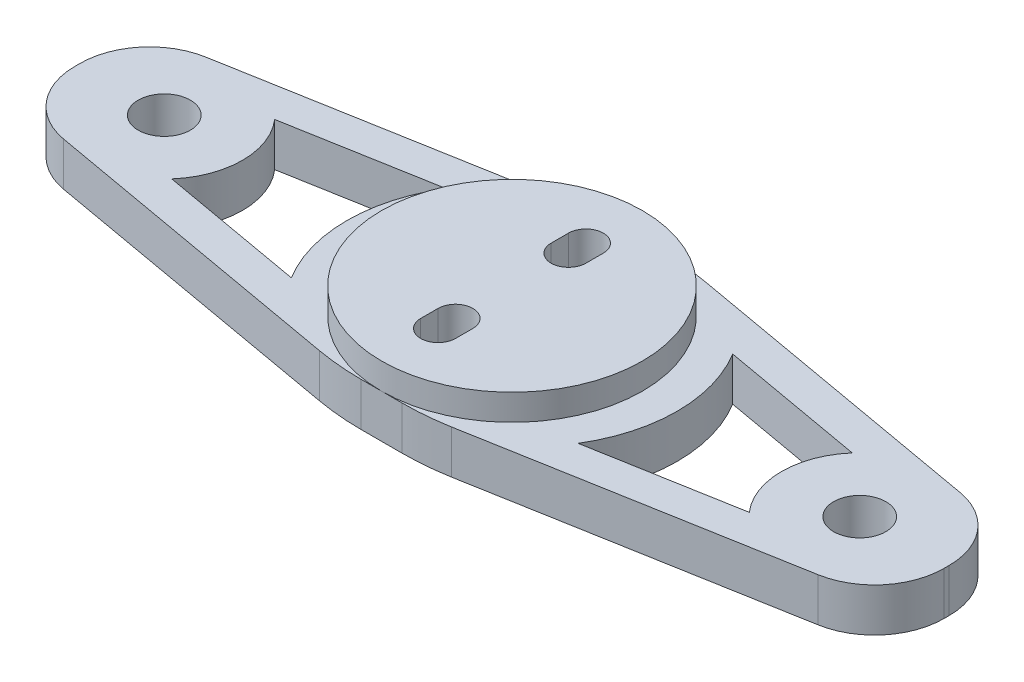
SolidWorks part; units mm, degrees
ref_plane "Front Plane" through (0, 0, 0) normal (0, 0, 1) x (1, 0, 0)
ref_plane "Top Plane" through (0, 0, 0) normal (0, 1, 0) x (1, 0, 0)
ref_plane "Right Plane" through (0, 0, 0) normal (1, 0, 0) x (0, 0, -1)
sketch "Sketch1" plane through (0, 0, 0) normal (0, 1, 0) x (1, 0, 0)
  line L1 (-50, -15) -> (50, -15)
  line L2 (-50, -15) -> (-50, 15)
  line L3 (-50, 15) -> (50, 15)
  line L4 (50, -15) -> (50, 15)
  line L5 (-50, -15) -> (50, 15) construction
  line L6 (-50, 15) -> (50, -15) construction
  point P0 (0, 0)
  dimension "D1" = 30
  dimension "D2" = 100
extrude "Boss-Extrude1" add sketch "Sketch1" along normal blind 5
sketch "Sketch2" plane through (0, 5, 0) normal (0, 1, 0) x (1, 0, 0)
  circle A0 centre (0, 0) radius 15
extrude "Boss-Extrude2" add sketch "Sketch2" along normal blind 3
sketch "Sketch3" plane through (0, 8, 0) normal (0, 1, 0) x (1, 0, 0)
  line L0 (0, 6.5) -> (0, -6.5) construction
  line L1 (-2, 6.5) -> (-2, 8.5)
  line L2 (2, 6.5) -> (2, 8.5)
  line L3 (-2, -8.5) -> (-2, -6.5)
  line L4 (2, -8.5) -> (2, -6.5)
  arc A0 (-2, 6.5) -> (2, 6.5) centre (0, 6.5) ccw
  arc A1 (2, -6.5) -> (-2, -6.5) centre (0, -6.5) ccw
  arc A2 (2, 8.5) -> (-2, 8.5) centre (0, 8.5) ccw
  arc A3 (-2, -8.5) -> (2, -8.5) centre (0, -8.5) ccw
  dimension "D1" = 4
  dimension "D3" = 6.5
  dimension "D2" = 6.5
extrude "Cut-Extrude1" cut sketch "Sketch3" against normal through all
sketch "Sketch4" plane through (0, 5, 0) normal (0, 1, 0) x (1, 0, 0)
  line L0 (-40, 0) -> (40, 0) construction
  circle A0 centre (40, 0) radius 3
  circle A1 centre (-40, 0) radius 3
  dimension "D1" = 80
  dimension "D2" = 6
extrude "Cut-Extrude2" cut sketch "Sketch4" against normal through all
chamfer "Chamfer1" distance 8 distance2 45 1 edges at (50, 2.5, -15)
chamfer "Chamfer2" distance 45 distance2 8 1 edges at (50, 2.5, 15)
chamfer "Chamfer3" distance 45 distance2 8 1 edges at (-50, 2.5, -15)
chamfer "Chamfer4" distance 8 distance2 45 1 edges at (-50, 2.5, 15)
fillet "Fillet1" radius 8 4 edges at (-50, 2.5, -7) (-50, 2.5, 7) (50, 2.5, 7) (50, 2.5, -7)
sketch "Sketch5" plane through (0, 5, 0) normal (0, 1, 0) x (1, 0, 0)
  line L0 (-40, 0) -> (-19, 0) construction
  line L2 (-4.2999, 11.0617) -> (-42.7001, 4.235)
  line L3 (-16.4871, 8.8951) -> (-33.2212, 5.9202)
  line L5 (-42.7001, -4.235) -> (-4.2999, -11.0617)
  line L6 (-33.2212, -5.9202) -> (-16.4871, -8.8951)
  arc A2 (-16.4871, 8.8951) -> (-16.4871, -8.8951) centre (-2, 0) ccw
  circle A6 centre (-40, 0) radius 9
  arc A7 (-33.2212, -5.9202) -> (-33.2212, 5.9202) centre (-40, 0) ccw
  dimension "D1" = 17
  dimension "D5" = 21
  dimension "D2" = 6
  dimension "D3" = 4
  dimension "D4" = 4
extrude "Cut-Extrude3" cut sketch "Sketch5" against normal through all
mirror "Mirror2" about plane through (0, 0, 0) normal (1, 0, 0) of "Cut-Extrude3"
fillet "Fillet2" radius 30 4 edges at (5, 2.5, -15) (-5, 2.5, -15) (-5, 2.5, 15) (5, 2.5, 15)
sketch "Sketch7" plane through (0, 0, 0) normal (0, -1, 0) x (1, 0, 0)
  line L6 (-4, 8.5) -> (-4, 6.5)
  line L7 (4, 6.5) -> (4, 8.5)
  line L8 (-4, 8.5) -> (-4, 6.5)
  line L9 (4, 6.5) -> (4, 8.5)
  arc A8 (4, 8.5) -> (-4, 8.5) centre (0, 8.5) ccw
  arc A9 (-4, 6.5) -> (4, 6.5) centre (0, 6.5) ccw
  arc A10 (4, 8.5) -> (-4, 8.5) centre (0, 8.5) ccw
  arc A11 (-4, 6.5) -> (4, 6.5) centre (0, 6.5) ccw
  dimension "D1" = 2
extrude "Cut-Extrude4" cut sketch "Sketch7" against normal blind 3
mirror "Mirror3" about plane through (0, 0, 0) normal (0, 0, 1) of "Cut-Extrude4"
fillet "Fillet3" radius 0.5 8 edges at (-4, 0, -7.5) (0, 0, -12.5) (4, 0, -7.5) (4, 0, 7.5) (0, 0, 2.5) (-4, 0, 7.5) (0, 0, -2.5) (0, 0, 12.5)
